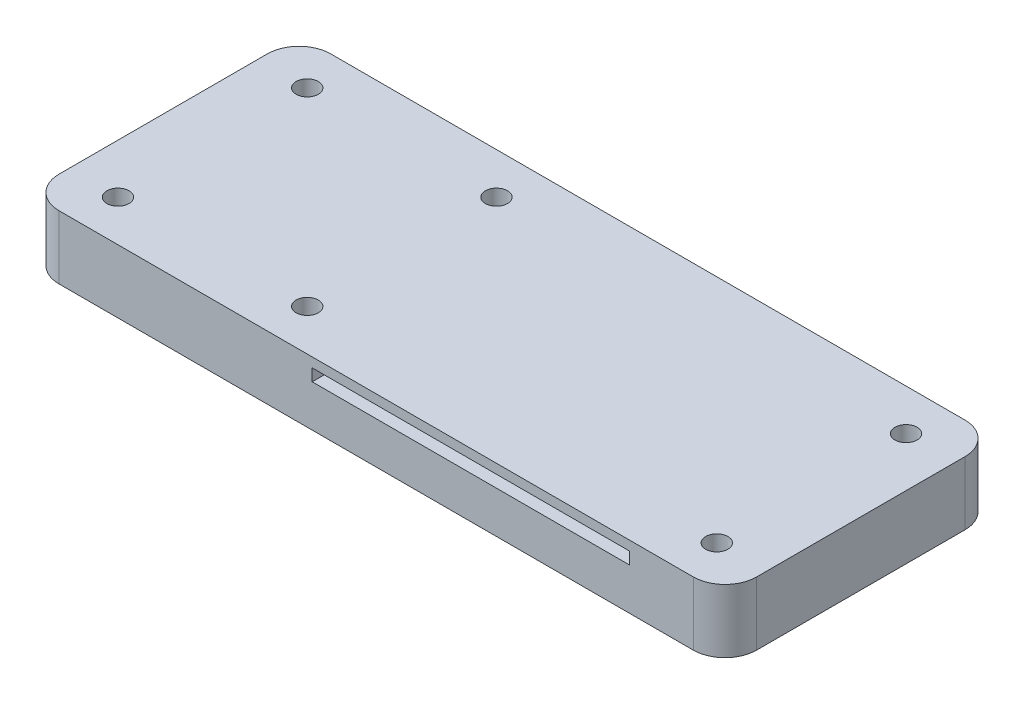
SolidWorks part; units mm, degrees
ref_plane "Front Plane" through (0, 0, 0) normal (0, 0, 1) x (1, 0, 0)
ref_plane "Top Plane" through (0, 0, 0) normal (0, 1, 0) x (1, 0, 0)
ref_plane "Right Plane" through (0, 0, 0) normal (1, 0, 0) x (0, 0, -1)
sketch "Sketch1" plane through (0, 0, 0) normal (0, 1, 0) x (1, 0, 0)
  line L0 (47.21, 14.92) -> (47.21, -14.92) construction
  line L1 (-50, -21.42) -> (50, -21.42)
  line L2 (-55, -16.42) -> (-55, 16.42)
  line L3 (-50, 21.42) -> (50, 21.42)
  line L4 (55, -16.42) -> (55, 16.42)
  line L5 (-55, -21.42) -> (55, 21.42) construction
  line L6 (-55, 21.42) -> (55, -21.42) construction
  line L7 (-47.21, 14.92) -> (-17.37, 14.92) construction
  line L8 (-47.21, 14.92) -> (-47.21, -14.92) construction
  line L9 (-47.21, -14.92) -> (-17.37, -14.92) construction
  line L10 (-17.37, 14.92) -> (-17.37, -14.92) construction
  line L11 (-47.21, 0) -> (47.21, 0) construction
  arc A0 (-55, -16.42) -> (-50, -21.42) centre (-50, -16.42) ccw
  arc A1 (50, -21.42) -> (55, -16.42) centre (50, -16.42) ccw
  arc A2 (55, 16.42) -> (50, 21.42) centre (50, 16.42) ccw
  arc A3 (-50, 21.42) -> (-55, 16.42) centre (-50, 16.42) ccw
  circle A4 centre (-47.21, 14.92) radius 1.75
  circle A5 centre (-17.37, 14.92) radius 1.75
  circle A6 centre (-17.37, -14.92) radius 1.75
  circle A7 centre (-47.21, -14.92) radius 1.75
  circle A8 centre (47.21, 14.92) radius 1.75
  circle A9 centre (47.21, -14.92) radius 1.75
  point P0 (0, 0)
  point P22 (-17.37, 0)
  dimension "D1" = 5
  dimension "D5" = 3.5
  dimension "D2" = 110
  dimension "D3" = 42.84
  dimension "D4" = 42.2
  dimension "D6" = 64.58
extrude "Boss-Extrude1" add sketch "Sketch1" along normal mid plane 10
sketch "Sketch2" plane through (0, 0, 21.42) normal (0, 0, 1) x (1, 0, 0)
  line L0 (-15.62, 5) -> (-19.12, 5) construction
  line L1 (-10.08, 3.5) -> (39.92, 3.5)
  line L2 (-10.08, 3.5) -> (-10.08, 1.6)
  line L3 (-10.08, 1.6) -> (39.92, 1.6)
  line L4 (39.92, 3.5) -> (39.92, 1.6)
  line L5 (48.96, 5) -> (45.46, 5) construction
  line L6 (-15.62, 5) -> (-19.12, 5) construction
  line L7 (48.96, 5) -> (45.46, 5) construction
  line L8 (-15.62, 2.55) -> (-10.08, 2.55) construction
  line L9 (39.92, 2.55) -> (45.46, 2.55) construction
  line L10 (-50, 5) -> (50, 5) construction
  point P4 (0, 0)
  dimension "D1" = 1.9
  dimension "D2" = 1.5
  dimension "D3" = 50
extrude "Cut-Extrude1" cut sketch "Sketch2" against normal through all
